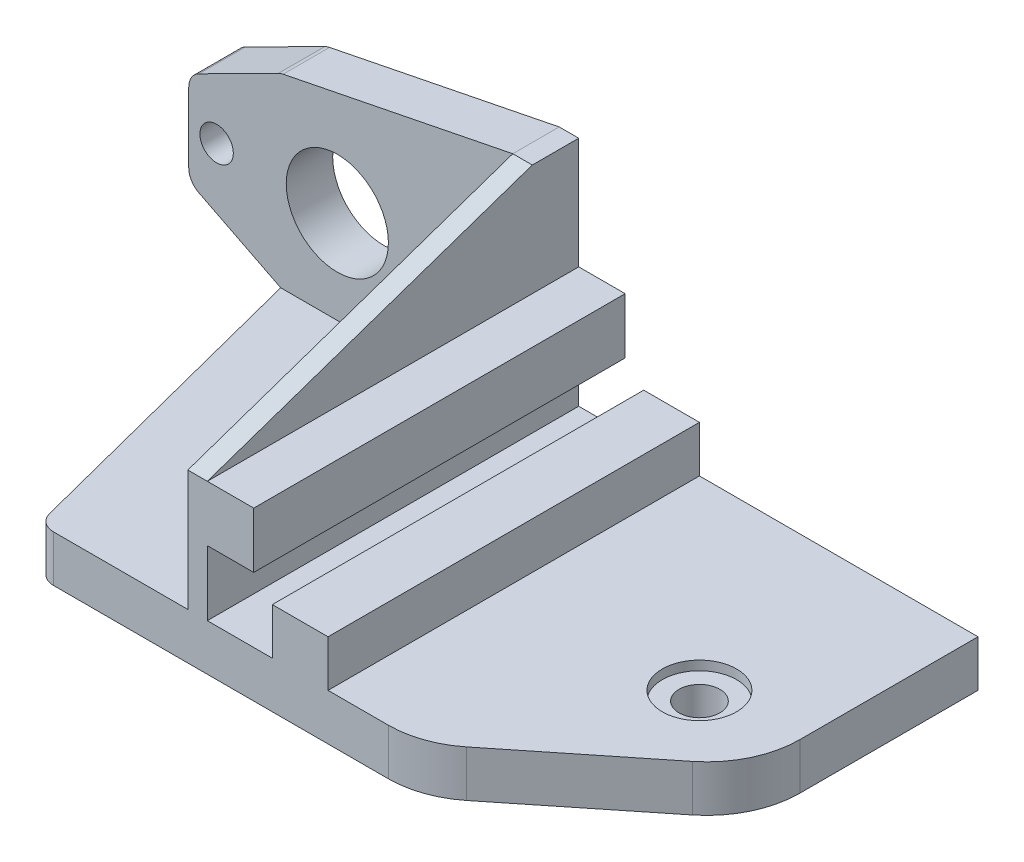
SolidWorks part; units mm, degrees
ref_plane "Plan de face" through (0, 0, 0) normal (0, 0, 1) x (1, 0, 0)
ref_plane "Plan de dessus" through (0, 0, 0) normal (0, 1, 0) x (1, 0, 0)
ref_plane "Plan de droite" through (0, 0, 0) normal (1, 0, 0) x (0, 0, -1)
sketch "Esquisse1" plane through (0, 0, 0) normal (0, 0, 1) x (1, 0, 0)
  line L1 (-25, 15) -> (25, 15)
  line L2 (-25, 15) -> (-25, -15)
  line L3 (-25, -15) -> (25, -15)
  line L4 (25, 15) -> (25, -15)
  dimension "D1" = 30
  dimension "D2" = 15
  dimension "D3" = 50
  dimension "D4" = 25
extrude "Boss.-Extru.1" add sketch "Esquisse1" along normal blind 40
sketch "Esquisse2" plane through (0, 0, 40) normal (0, 0, 1) x (1, 0, 0)
  line L0 (25, -15) -> (25, 15) construction
  line L1 (12, -10) -> (19, -10)
  line L2 (12, -10) -> (12, -3)
  line L3 (12, -3) -> (19, -3)
  line L4 (19, -10) -> (19, -3)
  line L5 (12, 10) -> (19, 10)
  line L6 (12, 10) -> (12, 3)
  line L7 (12, 3) -> (19, 3)
  line L8 (19, 10) -> (19, 3)
  line L10 (25, 15) -> (-25, 15) construction
  dimension "D1" = 7
  dimension "D2" = 7
  dimension "D3" = 7
  dimension "D4" = 7
  dimension "D5" = 6
  dimension "D6" = 6
  dimension "D7" = 6
  dimension "D8" = 5
extrude "Enlèv. mat.-Extru.1" cut sketch "Esquisse2" against normal through all
sketch "Esquisse3" plane through (0, 0, 40) normal (0, 0, 1) x (1, 0, 0)
  line L0 (25, -15) -> (25, 15) construction
  line L1 (17, 5) -> (25, 5)
  line L2 (17, 5) -> (17, -5)
  line L3 (17, -5) -> (25, -5)
  line L4 (25, 5) -> (25, -5)
  line L5 (12, -3) -> (12, -10) construction
  line L6 (12, -10) -> (19, -10) construction
  line L9 (19, 10) -> (12, 10) construction
  dimension "D1" = 5
  dimension "D2" = 5
  dimension "D3" = 5
extrude "Enlèv. mat.-Extru.2" cut sketch "Esquisse3" against normal through all
sketch "Esquisse5" plane through (0, 0, 40) normal (0, 0, 1) x (1, 0, 0)
  line L0 (-25, -15) -> (25, -15) construction
  line L1 (-25, 15) -> (9.9, 15)
  line L2 (-25, 15) -> (-25, -15)
  line L3 (-25, -15) -> (9.9, -15)
  line L4 (9.9, 15) -> (9.9, -15)
  dimension "D1" = 2.1
extrude "Enlèv. mat.-Extru.4" cut sketch "Esquisse5" against normal blind 35
sketch "Esquisse7" plane through (0, 0, 0) normal (0, 0, -1) x (-1, 0, 0)
  line L2 (25, -15) -> (-25, -15) construction
  circle A0 centre (9, 0) radius 5.5
  circle A1 centre (22, 0) radius 1.8
  circle A2 centre (-4, 0) radius 1.8
  dimension "D1" = 11
  dimension "D4" = 3.6
  dimension "D5" = 3.6
  dimension "D2" = 21
  dimension "D3" = 15
  dimension "D6" = 13
  dimension "D7" = 13
  dimension "D8" = 15
  dimension "D9" = 15
extrude "Enlèv. mat.-Extru.6" cut sketch "Esquisse7" against normal through all
sketch "Esquisse9" plane through (0, -15, 0) normal (0, -1, 0) x (1, 0, 0)
  line L0 (9.9, 40) -> (-6.1, 40)
  line L1 (-6.1, 40) -> (-15.1, 5)
  line L2 (-25, 5) -> (9.9, 5) construction
  line L3 (-15.1, 5) -> (9.9, 5)
  line L4 (9.9, 5) -> (9.9, 40)
  dimension "D1" = 16
  dimension "D2" = 25
extrude "Boss.-Extru.2" add sketch "Esquisse9" against normal blind 5
sketch "Esquisse10" plane through (0, -15, 0) normal (0, -1, 0) x (1, 0, 0)
  line L0 (-6.1, 40) -> (25, 40) construction
  line L1 (25, 40) -> (25, 0) construction
  circle A0 centre (5, 20) radius 2.1
  dimension "D1" = 4.2
  dimension "D2" = 20
  dimension "D3" = 20
extrude "Enlèv. mat.-Extru.7" cut sketch "Esquisse10" against normal through all
sketch "Esquisse11" plane through (0, -10, 0) normal (0, 1, 0) x (1, 0, 0)
  circle A0 centre (5, -20) radius 4
extrude "Enlèv. mat.-Extru.8" cut sketch "Esquisse11" against normal blind 1
sketch "Esquisse13" plane through (0, 0, 5) normal (0, 0, 1) x (1, 0, 0)
  line L0 (-15.1, -15) -> (-15.1, -10)
  line L1 (-15.1, -10) -> (-25, -5)
  line L2 (-25, 15) -> (-25, -15) construction
  line L3 (-25, -5) -> (-25, -15)
  line L4 (-25, -15) -> (-15.1, -15)
  line L5 (-25, 5) -> (-15.1, 10)
  line L6 (-15.1, 10) -> (9.9, 15)
  line L7 (9.9, 15) -> (-25, 15)
  line L8 (-25, 15) -> (-25, 5)
  dimension "D1" = 10
  dimension "D2" = 10
  dimension "D3" = 5
  dimension "D4" = 9.9
extrude "Enlèv. mat.-Extru.9" cut sketch "Esquisse13" against normal through all
fillet "Congé2" radius 2 4 edges at (-6.1, -12.5, 40) (-15.1, 10, 2.5) (-25, 5, 2.5) (-25, -5, 2.5)
sketch "Esquisse14" plane through (0, 0, 40) normal (0, 0, 1) x (1, 0, 0)
  line L1 (25, 15) -> (12, 15)
  line L2 (25, 15) -> (25, 3)
  line L3 (25, 3) -> (12, 3)
  line L4 (12, 15) -> (12, 3)
extrude "Enlèv. mat.-Extru.10" cut sketch "Esquisse14" against normal through all
sketch "Esquisse15" plane through (25, 0, 0) normal (1, 0, 0) x (0, 0, -1)
  line L0 (-40, -15) -> (-40, -5) construction
  line L1 (0, -15) -> (-40, -15)
  line L2 (0, -15) -> (0, -10)
  line L3 (0, -10) -> (-40, -10)
  line L4 (-40, -15) -> (-40, -10)
  dimension "D1" = 5
extrude "Boss.-Extru.3" add sketch "Esquisse15" along normal blind 30
sketch "Esquisse16" plane through (0, -10, 0) normal (0, 1, 0) x (1, 0, 0)
  line L0 (55, 0) -> (55, -40) construction
  line L1 (55, -40) -> (25, -40) construction
  circle A0 centre (45, -20) radius 2.2
  dimension "D2" = 4.4
  dimension "D1" = 10
  dimension "D3" = 20
extrude "Enlèv. mat.-Extru.11" cut sketch "Esquisse16" against normal through all
sketch "Esquisse17" plane through (0, -10, 0) normal (0, 1, 0) x (1, 0, 0)
  circle A0 centre (45, -20) radius 4
  circle A1 centre (5, -20) radius 4 construction
extrude "Enlèv. mat.-Extru.12" cut sketch "Esquisse17" against normal blind 1
chamfer "Chanfrein1" distance 20 distance2 16 1 edges at (55, -12.5, 40)
fillet "Congé3" radius 10 1 edges at (55, -12.5, 24)
chamfer "Chanfrein2" distance 35 distance2 12 1 edges at (10.95, 15, 40)
fillet "Congé4" radius 10 1 edges at (35, -12.5, 40)
